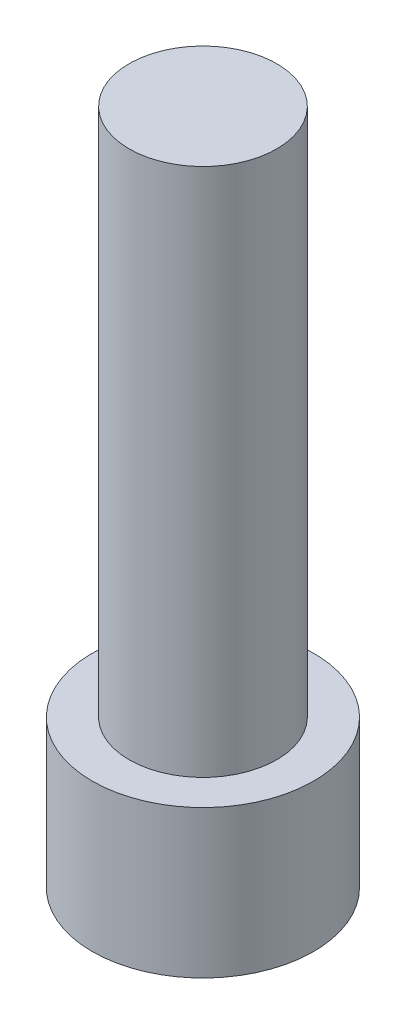
SolidWorks part; units mm, degrees
material "AISI 304"
ref_plane "Alzado" through (0, 0, 0) normal (0, 0, 1) x (1, 0, 0)
ref_plane "Planta" through (0, 0, 0) normal (0, 1, 0) x (1, 0, 0)
ref_plane "Vista lateral" through (0, 0, 0) normal (1, 0, 0) x (0, 0, -1)
sketch "Croquis1" plane through (0, 0, 0) normal (0, 1, 0) x (1, 0, 0)
  circle A0 centre (0, 0) radius 4.5
  dimension "D1" = 9
extrude "Saliente-Extruir1" add sketch "Croquis1" along normal blind 6
sketch "Croquis2" plane through (0, 6, 0) normal (0, 1, 0) x (1, 0, 0)
  circle A0 centre (0, 0) radius 3
  dimension "D1" = 6
extrude "Saliente-Extruir2" add sketch "Croquis2" along normal blind 21.5
sketch "Croquis3" plane through (0, 0, 0) normal (0, -1, 0) x (1, 0, 0)
  line L1 (2.8868, 0) -> (1.4434, 2.5)
  line L2 (1.4434, 2.5) -> (-1.4434, 2.5)
  line L3 (-1.4434, 2.5) -> (-2.8868, 0)
  line L4 (-2.8868, 0) -> (-1.4434, -2.5)
  line L5 (-1.4434, -2.5) -> (1.4434, -2.5)
  line L6 (1.4434, -2.5) -> (2.8868, 0)
  circle A0 centre (0, 0) radius 2.5 construction
  dimension "D1" = 5
extrude "Cortar-Extruir1" cut sketch "Croquis3" against normal blind 5
